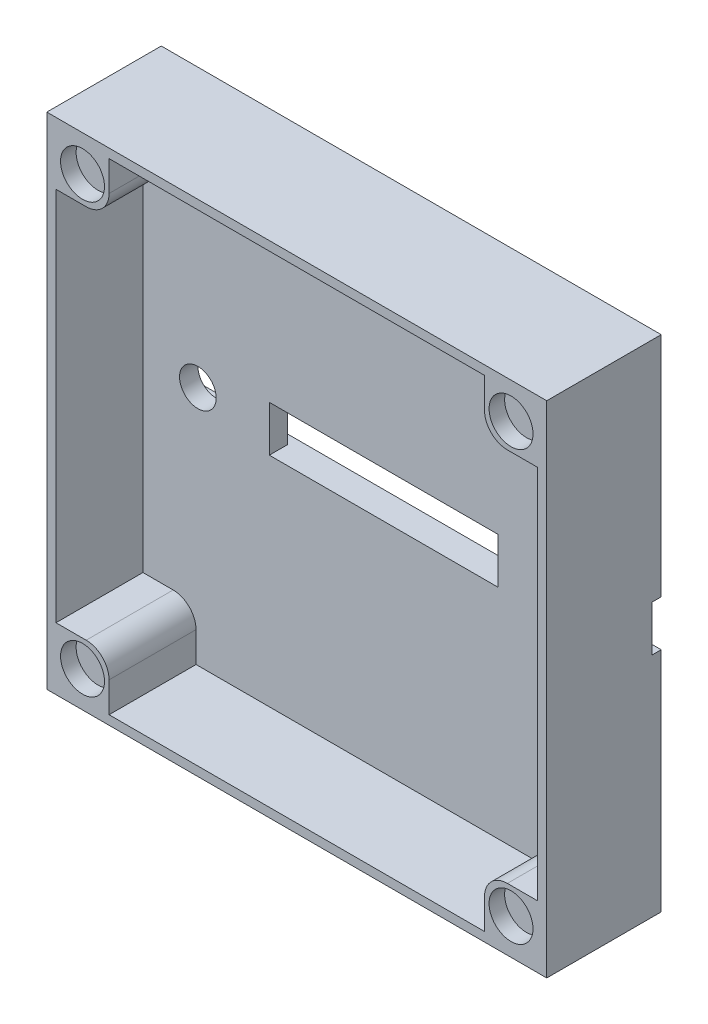
SolidWorks part; units mm, degrees
ref_plane "Přední rovina" through (0, 0, 0) normal (0, 0, 1) x (1, 0, 0)
ref_plane "Horní rovina" through (0, 0, 0) normal (0, 1, 0) x (1, 0, 0)
ref_plane "Pravá rovina" through (0, 0, 0) normal (1, 0, 0) x (0, 0, -1)
sketch "Skica1" plane through (0, 0, 0) normal (0, 0, 1) x (1, 0, 0)
  line L1 (27.3, 27.3) -> (-27.3, 27.3)
  line L2 (27.3, 27.3) -> (27.3, -27.3)
  line L3 (27.3, -27.3) -> (-27.3, -27.3)
  line L4 (-27.3, 27.3) -> (-27.3, -27.3)
  line L5 (27.3, 27.3) -> (-27.3, -27.3) construction
  line L6 (27.3, -27.3) -> (-27.3, 27.3) construction
  point P0 (0, 0)
  point P5 (-27.5, 0)
  point P11 (4.5, 0)
  dimension "D1" = 54.6
  dimension "D2" = 54.6
extrude "Přidat vysunutím2" add sketch "Skica1" along normal blind 3 contours L2 L1 L4 L3
sketch "Skica4" plane through (0, 0, 3) normal (0, 0, 1) x (1, 0, 0)
  line L1 (-12.5, 2.5) -> (12.5, 2.5)
  line L2 (-12.5, 2.5) -> (-12.5, -2.5)
  line L3 (-12.5, -2.5) -> (12.5, -2.5)
  line L4 (12.5, 2.5) -> (12.5, -2.5)
  line L5 (-12.5, 2.5) -> (12.5, -2.5) construction
  line L6 (-12.5, -2.5) -> (12.5, 2.5) construction
  line L10 (-27.3, 27.3) -> (-27.3, -27.3) construction
  point P0 (0, 0)
  dimension "D1" = 5
  dimension "D2" = 25
  dimension "D3" = 14.8
extrude "Odebrat vysunutím1" cut sketch "Skica4" against normal blind 2
sketch "Skica5" plane through (0, 0, 0) normal (0, 0, -1) x (-1, 0, 0)
  line L10 (27.3, 27.3) -> (27.3, -27.3) construction
  line L11 (-27.3, 2.5) -> (27.3, 2.5)
  line L12 (-27.3, 2.5) -> (-27.3, -2.5)
  line L13 (-27.3, -2.5) -> (27.3, -2.5)
  line L14 (27.3, 2.5) -> (27.3, -2.5)
  line L15 (-27.3, 2.5) -> (27.3, -2.5) construction
  line L16 (-27.3, -2.5) -> (27.3, 2.5) construction
  point P0 (0, 0)
  dimension "D1" = 5
extrude "Odebrat vysunutím3" cut sketch "Skica5" against normal blind 1 contours L11 L14 L13 L12
sketch "Skica14" plane through (0, 0, 3) normal (0, 0, 1) x (1, 0, 0)
  line L1 (-27.3, 27.3) -> (27.3, 27.3)
  line L2 (-27.3, 27.3) -> (-27.3, -27.3)
  line L3 (-27.3, -27.3) -> (27.3, -27.3)
  line L4 (27.3, 27.3) -> (27.3, -27.3)
  line L5 (-26.3, 26.3) -> (26.3, 26.3)
  line L6 (-26.3, 26.3) -> (-26.3, -27.3)
  line L7 (-26.3, -27.3) -> (26.3, -27.3)
  line L8 (26.3, 26.3) -> (26.3, -27.3)
  line L9 (-26.3, -27.3) -> (26.3, -27.3)
  line L10 (-26.3, -27.3) -> (-26.3, -26.3)
  line L12 (26.3, -27.3) -> (26.3, -26.3)
  line L13 (-26.3, -27.3) -> (26.3, -27.3)
  line L14 (-26.3, -27.3) -> (-26.3, -26.3)
  line L15 (-26.3, -26.3) -> (26.3, -26.3)
  line L16 (26.3, -27.3) -> (26.3, -26.3)
  line M13 (-27.3, -27.3) -> (27.3, -27.3)
  line M14 (27.3, -27.3) -> (27.3, 27.3)
  line M15 (27.3, 27.3) -> (-27.3, 27.3)
  line M16 (-27.3, 27.3) -> (-27.3, -27.3)
  dimension "D1" = 1
  dimension "D2" = 1
  dimension "D3" = 1
  dimension "D4" = 0
  dimension "D5" = 1
  dimension "D6" = 52.6
extrude "Přidat vysunutím9" add sketch "Skica14" along normal blind 9.5 contours L5 L8 L6 M13 M14 M15 M16 | L14 L13 L16 L15
sketch "Skica17" plane through (0, 0, 1) normal (0, 0, -1) x (-1, 0, 0)
  line L0 (-27.3, 2.5) -> (-27.3, -2.5) construction
  line L1 (-12.5, -2.5) -> (-12.5, 2.5) construction
  line L2 (27.3, 2.5) -> (27.3, -2.5) construction
  circle A0 centre (-20.3, 0) radius 2
  circle A1 centre (20.3, 0) radius 2
  dimension "D1" = 4
  dimension "D2" = 4
  dimension "D3" = 7
  dimension "D4" = 7.8
  dimension "D5" = 7
extrude "Odebrat vysunutím8" cut sketch "Skica17" against normal blind 4
sketch "Skica19" plane through (0, 0, 0) normal (0, 0, -1) x (-1, 0, 0)
  line L1 (-27.3, 27.3) -> (-20.5, 27.3)
  line L2 (-27.3, 27.3) -> (-27.3, 20.5)
  line L3 (-27.3, 20.5) -> (-20.5, 20.5)
  line L4 (-20.5, 27.3) -> (-20.5, 20.5)
  line L5 (27.3, 27.3) -> (20.5, 27.3)
  line L6 (27.3, 27.3) -> (27.3, 20.5)
  line L7 (27.3, 20.5) -> (20.5, 20.5)
  line L8 (20.5, 27.3) -> (20.5, 20.5)
  line L9 (-27.3, -27.3) -> (-20.5, -27.3)
  line L10 (-27.3, -27.3) -> (-27.3, -20.5)
  line L11 (-27.3, -20.5) -> (-20.5, -20.5)
  line L12 (-20.5, -27.3) -> (-20.5, -20.5)
  line L13 (27.3, -27.3) -> (20.5, -27.3)
  line L14 (27.3, -27.3) -> (27.3, -20.5)
  line L15 (27.3, -20.5) -> (20.5, -20.5)
  line L16 (20.5, -27.3) -> (20.5, -20.5)
  dimension "D1" = 6.8
  dimension "D2" = 6.8
  dimension "D3" = 6.8
  dimension "D4" = 6.8
extrude "Přidat vysunutím10" add sketch "Skica19" against normal blind 12.5
sketch "Skica20" plane through (0, 0, 12.5) normal (0, 0, 1) x (1, 0, 0)
  line L0 (-27.3, -27.3) -> (27.3, -27.3) construction
  line L2 (-27.3, 27.3) -> (-27.3, -27.3) construction
  line L3 (27.3, 27.3) -> (-27.3, 27.3) construction
  line L4 (27.3, -27.3) -> (27.3, 27.3) construction
  line L5 (-27.3, -27.3) -> (27.3, -27.3) construction
  circle A0 centre (-23.4, -23.4) radius 2.4
  circle A1 centre (-23.4, 23.4) radius 2.4
  circle A2 centre (23.4003, 23.4) radius 2.4
  circle A3 centre (23.4003, -23.4) radius 2.4
  dimension "D1" = 4.8
  dimension "D4" = 4.8
  dimension "D5" = 3.9
  dimension "D7" = 4.8
  dimension "D10" = 4.8
  dimension "D2" = 3.9
  dimension "D3" = 3.9
  dimension "D6" = 3.9
  dimension "D8" = 3.8997
  dimension "D9" = 3.9
  dimension "D11" = 3.9
  dimension "D12" = 3.8997
extrude "Odebrat vysunutím9" cut sketch "Skica20" against normal blind 1.7
fillet "Zaoblit1" radius 2.5 4 edges at (20.5, 20.5, 7.75) (20.5, -20.5, 7.75) (-20.5, -20.5, 7.75) (-20.5, 20.5, 7.75)
